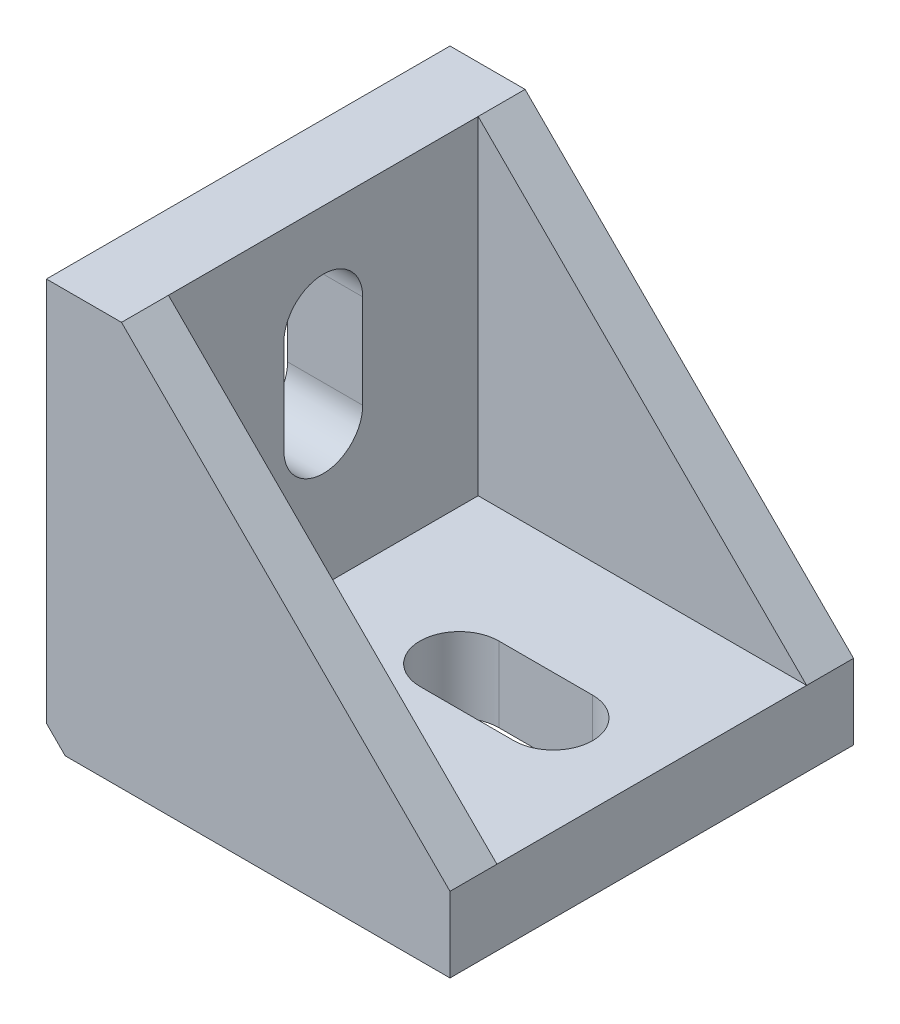
SolidWorks part; units mm, degrees
material "Alumina"
ref_plane "Front Plane" through (0, 0, 0) normal (0, 0, 1) x (1, 0, 0)
ref_plane "Top Plane" through (0, 0, 0) normal (0, 1, 0) x (1, 0, 0)
ref_plane "Right Plane" through (0, 0, 0) normal (1, 0, 0) x (0, 0, -1)
sketch "Esquisse1" plane through (0, 0, 0) normal (0, 0, 1) x (1, 0, 0)
  line L0 (0, 43) -> (0, 0)
  line L1 (0, 0) -> (43, 0)
  line L2 (43, 0) -> (43, 8)
  line L3 (43, 8) -> (8, 43)
  line L4 (8, 43) -> (0, 43)
  dimension "D1" = 43
  dimension "D2" = 43
  dimension "D3" = 8
  dimension "D4" = 8
extrude "Boss.-Extru.1" add sketch "Esquisse1" along normal blind 43
ref_plane "Plan1" through (0, 0, 21.5) normal (0, 0, 1) x (1, 0, 0)
sketch "Esquisse2" plane through (0, 0, 21.5) normal (0, 0, 1) x (1, 0, 0)
  line L0 (8, 43.5588) -> (8, 8)
  line L1 (8, 8) -> (47.7749, 8)
  line L2 (47.7749, 8) -> (49.4278, 41.5156)
  line L3 (49.4278, 41.5156) -> (8, 43.5588)
  line L6 (0, 43) -> (0, 0) construction
  line L7 (0, 0) -> (43, 0) construction
  dimension "D1" = 8
  dimension "D2" = 8
extrude "Enlèv. mat.-Extru.1" cut sketch "Esquisse2" against normal mid plane 33
sketch "Esquisse3" plane through (8, 0, 0) normal (1, 0, 0) x (0, 0, -1)
  line L5 (-21.5, 22.5) -> (-21.5, 32.5) construction
  line L7 (-25.7, 22.5) -> (-25.7, 32.5)
  line L8 (-17.3, 22.5) -> (-17.3, 32.5)
  line L9 (-5, 43) -> (-5, 8) construction
  line L10 (-38, 43) -> (-38, 8) construction
  line L11 (-43, 0) -> (0, 0) construction
  arc A1 (-25.7, 22.5) -> (-17.3, 22.5) centre (-21.5, 22.5) ccw
  arc A2 (-17.3, 32.5) -> (-25.7, 32.5) centre (-21.5, 32.5) ccw
  point P2 (-21.5, 27.5)
  point P7 (0, 0)
  dimension "D1" = 4.2
  dimension "D2" = 10
  dimension "D3" = 22.5
extrude "Enlèv. mat.-Extru.2" cut sketch "Esquisse3" along normal through all both and the other way through all
sketch "Esquisse4" plane through (0, 8, 0) normal (0, 1, 0) x (1, 0, 0)
  line L0 (8, -5) -> (43, -5) construction
  line L6 (32.5, -21.5) -> (22.5, -21.5) construction
  line L7 (32.5, -25.7) -> (22.5, -25.7)
  line L8 (32.5, -17.3) -> (22.5, -17.3)
  line L9 (8, -38) -> (43, -38) construction
  line L10 (0, -43) -> (0, 0) construction
  arc A0 (32.5, -25.7) -> (32.5, -17.3) centre (32.5, -21.5) ccw
  arc A1 (22.5, -17.3) -> (22.5, -25.7) centre (22.5, -21.5) ccw
  point P2 (27.5, -21.5)
  dimension "D1" = 4.2
  dimension "D2" = 10
  dimension "D3" = 22.5
extrude "Enlèv. mat.-Extru.3" cut sketch "Esquisse4" against normal through all
chamfer "Chanfrein1" distance 2 angle 45 1 edges at (0, 0, 21.5)
